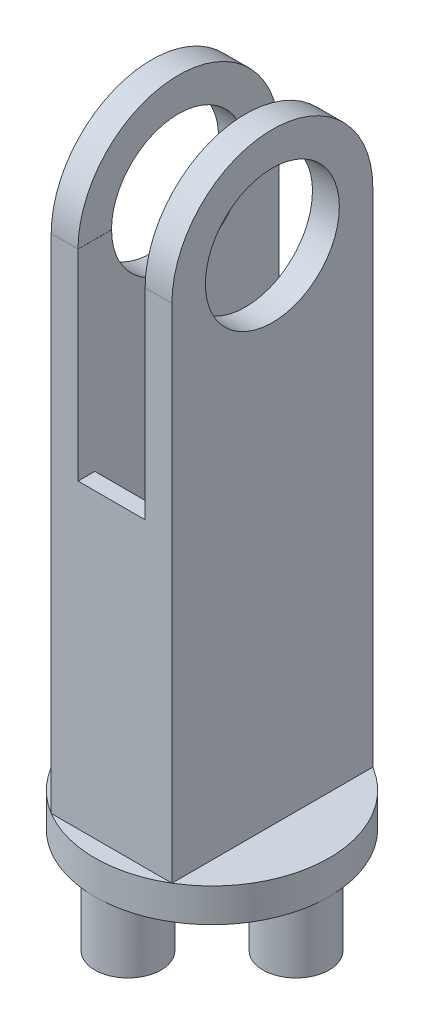
SolidWorks part; units mm, degrees
ref_plane "Front Plane" through (0, 0, 0) normal (0, 0, 1) x (1, 0, 0)
ref_plane "Top Plane" through (0, 0, 0) normal (0, 1, 0) x (1, 0, 0)
ref_plane "Right Plane" through (0, 0, 0) normal (1, 0, 0) x (0, 0, -1)
sketch "Sketch1" plane through (0, 0, 0) normal (0, 1, 0) x (1, 0, 0)
  line L0 (0, 35) -> (0, 25) construction
  circle A0 centre (0, 0) radius 35
extrude "Boss-Extrude1" add sketch "Sketch1" along normal blind 10
sketch "Sketch3" plane through (0, 0, 0) normal (0, -1, 0) x (1, 0, 0)
  line L0 (35, 0) -> (25.1, 0) construction
  circle A0 centre (0, 0) radius 35 construction
  circle A1 centre (25.1, 0) radius 9.9
  circle A2 centre (0, -25.1) radius 9.9
  circle A3 centre (-25.1, 0) radius 9.9
  circle A4 centre (0, 25.1) radius 9.9
  point P15 (0, 0)
  dimension "D1" = 4
extrude "Boss-Extrude2" add sketch "Sketch3" along normal blind 19
sketch "Sketch4" plane through (0, 10, 0) normal (0, 1, 0) x (1, 0, 0)
  line L1 (-18.0278, -30) -> (18.0278, -30)
  line L2 (-18.0278, -30) -> (-18.0278, 30)
  line L3 (-18.0278, 30) -> (18.0278, 30)
  line L4 (18.0278, -30) -> (18.0278, 30)
  line L5 (-18.0278, -30) -> (18.0278, 30) construction
  line L6 (-18.0278, 30) -> (18.0278, -30) construction
  circle A0 centre (0, 0) radius 35 construction
  circle A2 centre (0, 0) radius 35
  arc A3 (-18.0278, -30) -> (-18.0278, 30) centre (0, 0) ccw
  point P0 (0, 0)
  dimension "D1" = 0
extrude "Boss-Extrude8" add sketch "Sketch4" along normal blind 150 contours L1 L4 L3 L2
sketch "Sketch11" plane through (0, 160, 0) normal (0, 1, 0) x (1, 0, 0)
  line L0 (-18.0278, 30) -> (18.0278, 30) construction
  line L1 (-10, -30) -> (10, -30)
  line L2 (-10, -30) -> (-10, 30)
  line L3 (-10, 30) -> (10, 30)
  line L4 (10, -30) -> (10, 30)
  line L5 (-10, -30) -> (10, 30) construction
  line L6 (-10, 30) -> (10, -30) construction
  point P0 (0, 0)
extrude "Cut-Extrude2" cut sketch "Sketch11" against normal blind 60
sketch "Sketch12" plane through (0, 100, 0) normal (0, 1, 0) x (1, 0, 0)
  line L0 (10, -30) -> (10, 30) construction
  line L1 (-10, -25) -> (10, -25)
  line L2 (-10, -25) -> (-10, 25)
  line L3 (-10, 25) -> (10, 25)
  line L4 (10, -25) -> (10, 25)
  line L5 (-10, -25) -> (10, 25) construction
  line L6 (-10, 25) -> (10, -25) construction
  point P0 (0, 0)
extrude "Cut-Extrude3" cut sketch "Sketch12" against normal blind 90
sketch "Sketch13" plane through (-18.0278, 0, 0) normal (-1, 0, 0) x (0, 0, 1)
  line L0 (30, 160) -> (-30, 160) construction
  circle A0 centre (0, 160) radius 30
extrude "Boss-Extrude9" add sketch "Sketch13" against normal blind 8
sketch "Sketch14" plane through (18.0278, 0, 0) normal (1, 0, 0) x (0, 0, -1)
  line L0 (-30, 160) -> (30, 160) construction
  circle A0 centre (0, 160) radius 30
extrude "Boss-Extrude10" add sketch "Sketch14" against normal blind 8
sketch "Sketch15" plane through (18.0278, 0, 0) normal (1, 0, 0) x (0, 0, -1)
  circle A0 centre (0, 160) radius 20
extrude "Cut-Extrude4" cut sketch "Sketch15" against normal blind 97
